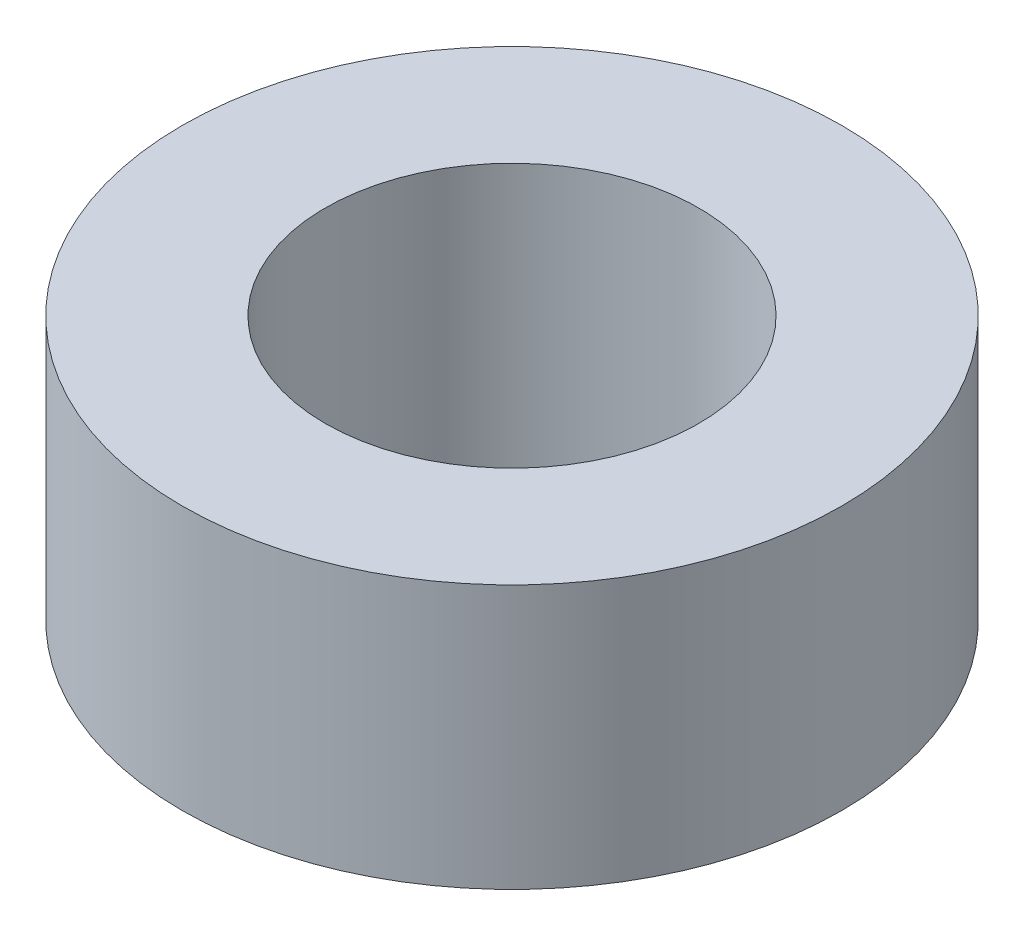
SolidWorks part; units mm, degrees
material "6061 Alloy"
ref_plane "Front Plane" through (0, 0, 0) normal (0, 0, 1) x (1, 0, 0)
ref_plane "Top Plane" through (0, 0, 0) normal (0, 1, 0) x (1, 0, 0)
ref_plane "Right Plane" through (0, 0, 0) normal (1, 0, 0) x (0, 0, -1)
sketch "Sketch1" plane through (0, 0, 0) normal (0, 1, 0) x (1, 0, 0)
  circle A0 centre (0, 0) radius 3.9688
  circle A1 centre (0, 0) radius 2.2479
  dimension "D1" = 4.4958
  dimension "D2" = 7.9375
extrude "Boss-Extrude1" add sketch "Sketch1" along normal blind 3.175
